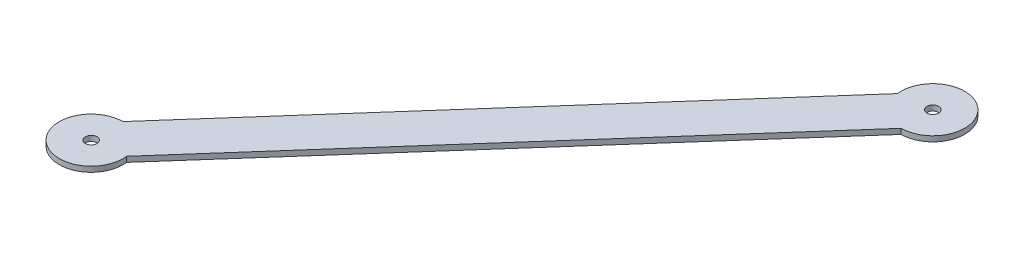
SolidWorks part; units mm, degrees
ref_plane "Front Plane" through (0, 0, 0) normal (0, 0, 1) x (1, 0, 0)
ref_plane "Top Plane" through (0, 0, 0) normal (0, 1, 0) x (1, 0, 0)
ref_plane "Right Plane" through (0, 0, 0) normal (1, 0, 0) x (0, 0, -1)
sketch "Sketch1" plane through (0, 0, 0) normal (0, 1, 0) x (1, 0, 0)
  line L0 (0, 19.1963) -> (98.7328, 131.1047)
  line L1 (-117.65, -133.35) -> (117.65, -133.35) construction
  line L2 (-117.65, -133.35) -> (-117.65, 133.35) construction
  line L3 (-117.65, 133.35) -> (117.65, 133.35) construction
  line L4 (117.65, -133.35) -> (117.65, 133.35) construction
  line L5 (-117.65, -133.35) -> (117.65, 133.35) construction
  line L6 (-117.65, 133.35) -> (117.65, -133.35) construction
  line L7 (0, 19.1963) -> (-98.7328, 131.1047)
  line L8 (16.9363, 0) -> (117.7795, -114.3004)
  line L9 (16.9363, 0) -> (117.7795, 114.3004)
  line L10 (0, -19.1963) -> (98.7328, -131.1047)
  line L11 (0, -19.1963) -> (-98.7328, -131.1047)
  line L12 (-117.7795, -114.3004) -> (-16.9363, 0)
  line L13 (-16.9363, 0) -> (-117.7795, 114.3004)
  line L14 (-16.9363, 0) -> (0, 19.1963) construction
  line L15 (0, 19.1963) -> (16.9363, 0) construction
  line L16 (-16.9363, 0) -> (0, 19.1963)
  line L17 (0, -19.1963) -> (16.9363, 0)
  circle A0 centre (117.65, 133.35) radius 3.5
  circle A1 centre (-117.65, 133.35) radius 3.5
  circle A2 centre (-117.65, -133.35) radius 3.5
  circle A3 centre (117.65, -133.35) radius 3.5
  circle A4 centre (117.65, 133.35) radius 19.05
  circle A5 centre (-117.65, 133.35) radius 19.05
  circle A6 centre (-117.65, -133.35) radius 19.05
  circle A7 centre (117.65, -133.35) radius 19.05
  point P0 (0, 0)
  point P21 (8.4681, 9.5982)
  point P23 (-8.4681, 9.5982)
  dimension "D3" = 7
  dimension "D6" = 38.1
  dimension "D1" = 235.3
  dimension "D2" = 266.7
  dimension "D5" = 25.4
extrude "Boss-Extrude1" add sketch "Sketch1" along normal blind 3.175 contours A6 L11 L17 L9 A4 L0 L16 L12 | A6 A2 | A0
